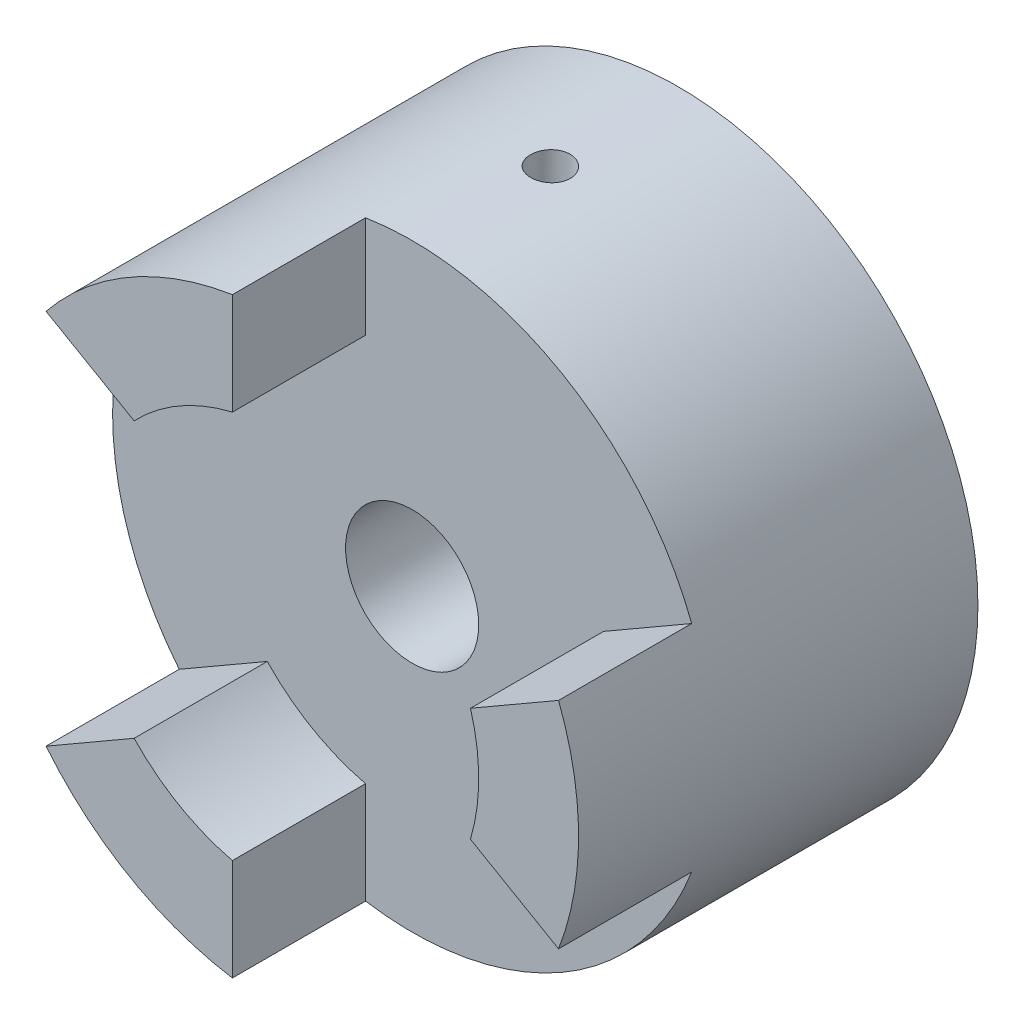
SolidWorks part; units mm, degrees
ref_plane "Front Plane" through (0, 0, 0) normal (0, 0, 1) x (1, 0, 0)
ref_plane "Top Plane" through (0, 0, 0) normal (0, 1, 0) x (1, 0, 0)
ref_plane "Right Plane" through (0, 0, 0) normal (1, 0, 0) x (0, 0, -1)
sketch "Sketch1" plane through (0, 0, 0) normal (0, 0, 1) x (1, 0, 0)
  circle A0 centre (0, 0) radius 22.5
  dimension "D1" = 45
extrude "Boss-Extrude1" add sketch "Sketch1" along normal blind 20
sketch "Sketch3" plane through (0, 0, 20) normal (0, 0, 1) x (1, 0, 0)
  circle A0 centre (0, 0) radius 5
  dimension "D1" = 10
extrude "Cut-Extrude1" cut sketch "Sketch3" against normal up to next
hole_wizard "Ø3.0mm Dowel Hole1" positions "3DSketch1" profile "Sketch4" hole size "Ø3.0" standard "ANSI Metric"
sketch3d "3DSketch1"
  point P0 (0.3326, 22.4975, 9.951)
sketch "Sketch4" plane through (0.3326, 22.4975, 9.951) normal (0, 0, 1) x (-0.9999, 0.0148, 0)
  line L0 (0, 0) -> (0, 22.9013)
  line L1 (0, 22.9013) -> (1.5, 22)
  line L2 (1.5, 22) -> (1.5, 0)
  line L5 (1.5, 0) -> (0, 0)
  line L10 (0, 22.9013) -> (-1.5, 22) construction
  line L11 (0, -6.35) -> (0, 107.95) construction
  dimension "Hole Dia." = 3
  dimension "Hole Depth" = 22
  dimension "Drill Angle" = 118
sketch "Sketch6" plane through (0, 0, 20) normal (0, 0, 1) x (1, 0, 0)
  line L0 (-3.5, 36.3116) -> (-3.5, -32.5042) construction
  line L1 (3.5, 36.3116) -> (3.5, -36.2663) construction
  line L2 (33.1967, -15.1247) -> (-26.3994, 19.2832) construction
  line L3 (29.6967, -21.1869) -> (-33.1575, 15.1021) construction
  line L4 (-29.6967, -21.1869) -> (29.8994, 13.221) construction
  line L5 (-33.1967, -15.1247) -> (29.6575, 21.1642) construction
  line L6 (-17.4984, 14.1441) -> (-10.8818, 10.3241)
  line L7 (-3.5, 22.2261) -> (-3.5, 14.586)
  line L8 (14.3818, 4.2619) -> (20.9984, 8.082)
  line L9 (20.9984, -8.082) -> (14.3818, -4.2619)
  line L10 (-3.5, -14.586) -> (-3.5, -22.2261)
  line L11 (-17.4984, -14.1441) -> (-10.8818, -10.3241)
  arc A0 (-3.5, 22.2261) -> (-17.4984, 14.1441) centre (0, 0) ccw
  arc A1 (-10.8818, -10.3241) -> (-3.5, -14.586) centre (0, 0) ccw
  arc A2 (-17.4984, -14.1441) -> (-3.5, -22.2261) centre (0, 0) ccw
  arc A3 (-3.5, 14.586) -> (-10.8818, 10.3241) centre (0, 0) ccw
  arc A4 (20.9984, -8.082) -> (20.9984, 8.082) centre (0, 0) ccw
  arc A5 (14.3818, -4.2619) -> (14.3818, 4.2619) centre (0, 0) ccw
  point P16 (0, 0)
  dimension "D3" = 30
  dimension "D4" = 45
  dimension "D1" = 7
  dimension "D2" = 3.5
extrude "Boss-Extrude3" add sketch "Sketch6" along normal blind 10
